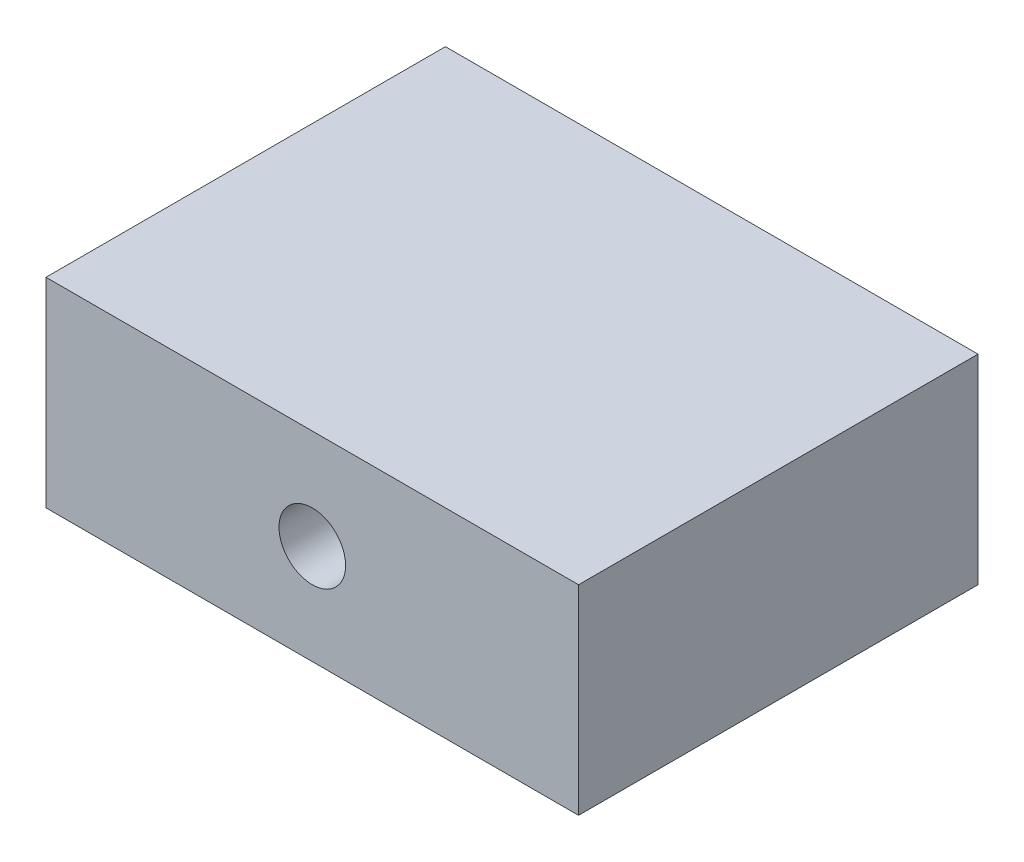
SolidWorks part; units mm, degrees
ref_plane "前视基准面" through (0, 0, 0) normal (0, 0, 1) x (1, 0, 0)
ref_plane "上视基准面" through (0, 0, 0) normal (0, 1, 0) x (1, 0, 0)
ref_plane "右视基准面" through (0, 0, 0) normal (1, 0, 0) x (0, 0, -1)
sketch "草图1" plane through (0, 0, 0) normal (0, 1, 0) x (1, 0, 0)
  line L1 (-40, 30) -> (40, 30)
  line L2 (-40, 30) -> (-40, -30)
  line L3 (-40, -30) -> (40, -30)
  line L4 (40, 30) -> (40, -30)
  line L5 (-40, 30) -> (40, -30) construction
  line L6 (-40, -30) -> (40, 30) construction
  point P0 (0, 0)
  dimension "D1" = 80
  dimension "D2" = 60
extrude "凸台-拉伸1" add sketch "草图1" along normal blind 30
sketch "草图2" plane through (0, 0, 30) normal (0, 0, 1) x (1, 0, 0)
  line L0 (-40, 30) -> (40, 0) construction
  line L1 (40, 30) -> (-40, 0) construction
  circle A0 centre (0, 15) radius 5
  dimension "D1" = 10
extrude "切除-拉伸1" cut sketch "草图2" against normal through all
